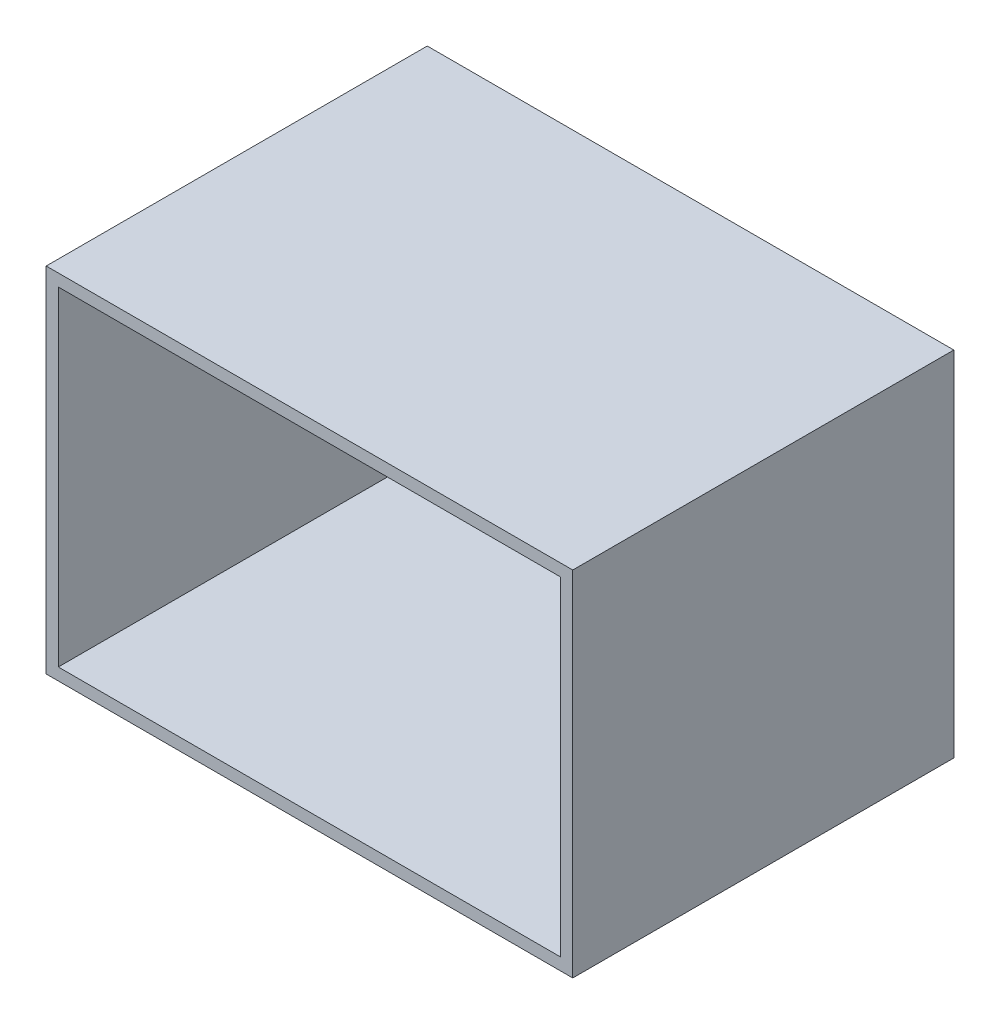
SolidWorks part; units mm, degrees
ref_plane "正面" through (0, 0, 0) normal (0, 0, 1) x (1, 0, 0)
ref_plane "平面" through (0, 0, 0) normal (0, 1, 0) x (1, 0, 0)
ref_plane "右側面" through (0, 0, 0) normal (1, 0, 0) x (0, 0, -1)
sketch "ｽｹｯﾁ1" plane through (0, 0, 0) normal (0, 0, 1) x (1, 0, 0)
  line L1 (-35.3566, 21.2746) -> (40.6434, 21.2746)
  line L2 (-35.3566, 21.2746) -> (-35.3566, -29.7254)
  line L3 (-35.3566, -29.7254) -> (40.6434, -29.7254)
  line L4 (40.6434, 21.2746) -> (40.6434, -29.7254)
  line L5 (-33.6066, 19.5246) -> (38.8934, 19.5246)
  line L6 (-33.6066, 19.5246) -> (-33.6066, -27.9754)
  line L7 (-33.6066, -27.9754) -> (38.8934, -27.9754)
  line L8 (38.8934, 19.5246) -> (38.8934, -27.9754)
  dimension "D1" = 76
  dimension "D2" = 51
  dimension "D3" = 72.5
  dimension "D4" = 47.5
  dimension "D5" = 1.75
  dimension "D6" = 1.75
extrude "ﾎﾞｽ - 押し出し1" add sketch "ｽｹｯﾁ1" along normal blind 55
